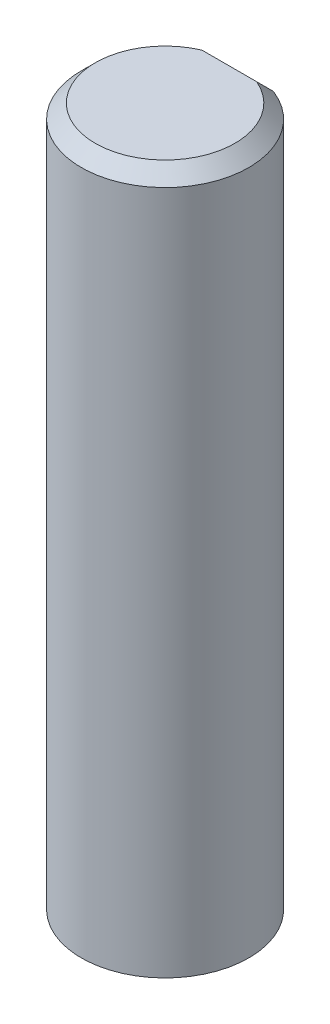
SolidWorks part; units mm, degrees
material "Chrome Stainless Steel"
ref_plane "Front Plane" through (0, 0, 0) normal (0, 0, 1) x (1, 0, 0)
ref_plane "Top Plane" through (0, 0, 0) normal (0, 1, 0) x (1, 0, 0)
ref_plane "Right Plane" through (0, 0, 0) normal (1, 0, 0) x (0, 0, -1)
ref_plane "Plane1" through (0, 25, 0) normal (0, 1, 0) x (1, 0, 0)
sketch "Sketch1" plane through (0, 25, 0) normal (0, 1, 0) x (1, 0, 0)
  line L0 (1.077, 2.8) -> (-1.077, 2.8)
  arc A0 (-1.077, 2.8) -> (1.077, 2.8) centre (0, 0) ccw
extrude "Boss-Extrude1" add sketch "Sketch1" against normal blind 25
chamfer "Chamfer1" distance 0.5 angle 45 2 edges at (0, 25, -2.8) (0, 25, 3)
